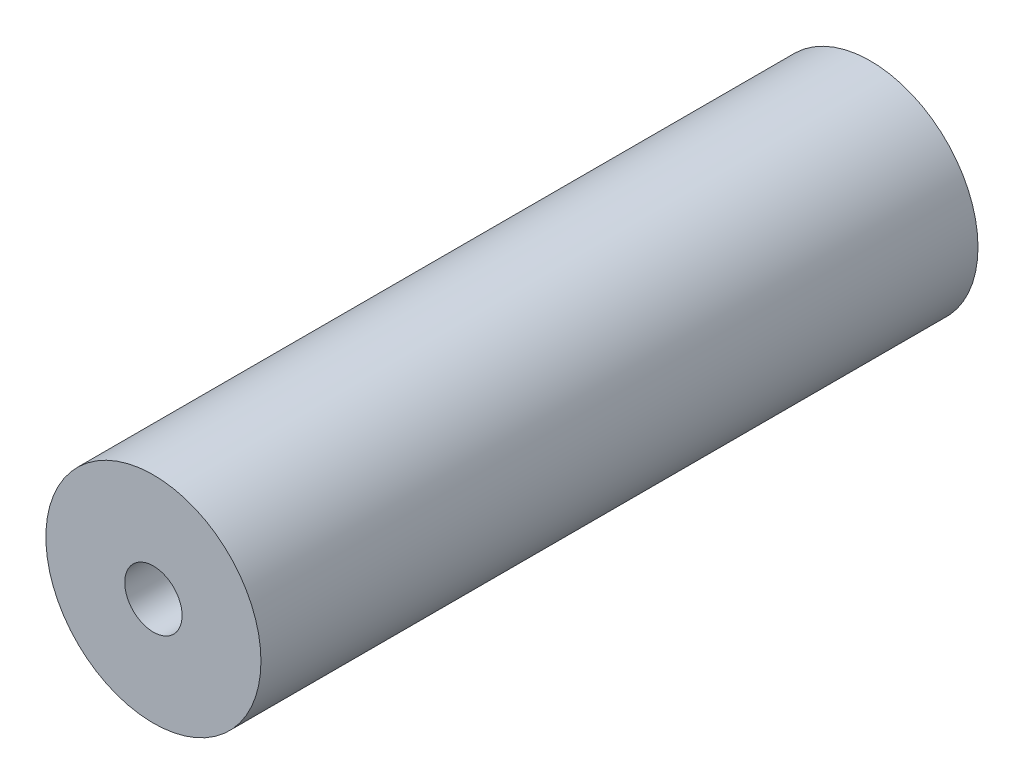
SolidWorks part; units mm, degrees
ref_plane "Спереди" through (0, 0, 0) normal (0, 0, 1) x (1, 0, 0)
ref_plane "Сверху" through (0, 0, 0) normal (0, 1, 0) x (1, 0, 0)
ref_plane "Справа" through (0, 0, 0) normal (1, 0, 0) x (0, 0, -1)
sketch "Эскиз1" plane through (0, 0, 0) normal (0, 0, 1) x (1, 0, 0)
  circle A0 centre (0, 0) radius 1.5
  circle A1 centre (0, 0) radius 0.4
  dimension "D1" = 0.8
  dimension "D2" = 3
extrude "Бобышка-Вытянуть1" add sketch "Эскиз1" along normal blind 10
